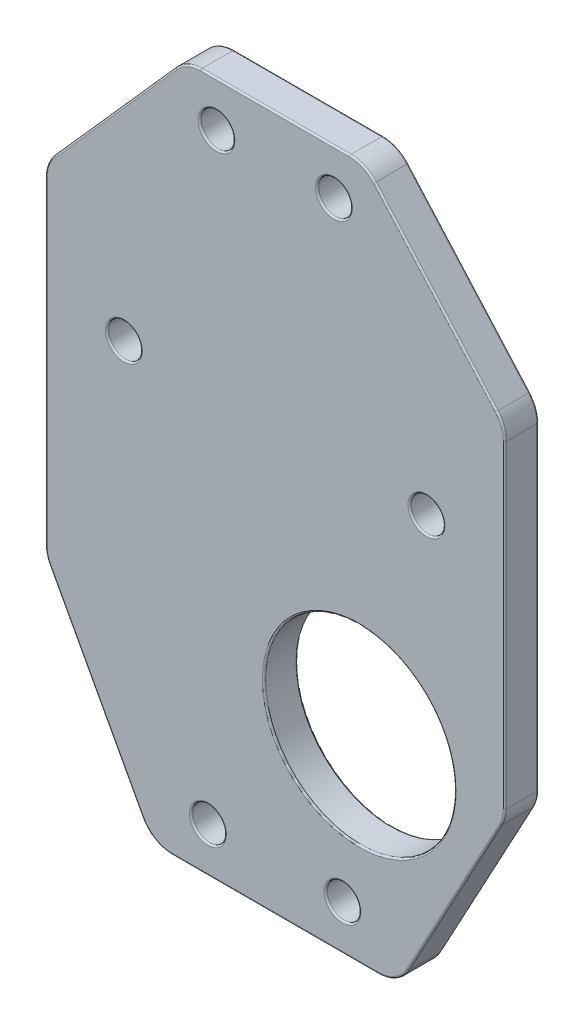
SolidWorks part; units mm, degrees
ref_plane "Front Plane" through (0, 0, 0) normal (0, 0, 1) x (1, 0, 0)
ref_plane "Top Plane" through (0, 0, 0) normal (0, 1, 0) x (1, 0, 0)
ref_plane "Right Plane" through (0, 0, 0) normal (1, 0, 0) x (0, 0, -1)
sketch "Sketch1" plane through (0, 0, 0) normal (0, 0, 1) x (1, 0, 0)
  line L0 (0, 0) -> (0, 62) construction
  line L1 (7.9898, 62) -> (-7.9898, 62)
  line L2 (-7.9898, 62) -> (-20.5, 47.8997)
  line L3 (-20.5, 47.8997) -> (-20.5, 17.5997)
  line L4 (-20.5, 17.5997) -> (-11, 0)
  line L5 (-11, 0) -> (0, 0)
  line L6 (20.5, 17.5997) -> (11, 0)
  line L7 (20.5, 47.8997) -> (20.5, 17.5997)
  line L8 (7.9898, 62) -> (20.5, 47.8997)
  line L9 (7.5, 17.5997) -> (20.5, 17.5997) construction
  line L10 (-13.5, 37.5997) -> (13.5, 37.5997) construction
  line L19 (0, 0) -> (11, 0)
  circle A0 centre (-6, 4) radius 1.5
  circle A1 centre (-13.5, 37.5997) radius 1.5
  circle A2 centre (-5.2398, 58) radius 1.5
  circle A3 centre (5.2398, 58) radius 1.5
  circle A4 centre (13.5, 37.5997) radius 1.5
  circle A5 centre (6, 4) radius 1.5
  circle A6 centre (7.5, 17.5997) radius 8.5
  circle A7 centre (7.5, 17.5997) radius 12 construction
  circle A8 centre (13.5, 37.5997) radius 5 construction
  circle A9 centre (-13.5, 37.5997) radius 5 construction
  dimension "D7" = 3
  dimension "D11" = 4
  dimension "D13" = 10.3
  dimension "D14" = 17
  dimension "D1" = 62
  dimension "D2" = 11
  dimension "D3" = 20
  dimension "D4" = 30.3
  dimension "D5" = 18.85
  dimension "D6" = 20.5
  dimension "D8" = 4
  dimension "D9" = 2.75
  dimension "D10" = 6
  dimension "D12" = 7
  dimension "D15" = 13
  dimension "D16" = 3.5
  dimension "D17" = 3.5
  dimension "D18" = 3.5
extrude "Boss-Extrude1" add sketch "Sketch1" along normal blind 3
fillet "Fillet1" radius 3 8 edges at (-11, 0, 1.5) (-20.5, 17.5997, 1.5) (-20.5, 47.8997, 1.5) (-7.9898, 62, 1.5) (7.9898, 62, 1.5) (20.5, 47.8997, 1.5) (11, 0, 1.5) (20.5, 17.5997, 1.5)
fillet "Fillet2" radius 0.15 46 edges at (16, 17.5997, 0) (12, 37.5997, 0) (-3.7398, 58, 0) (-4.5, 4, 0) (10.7472, 0.4237, 0) (15.9951, 9.2539, 0) (20.4086, 17.6228, 0) (20.5, 32.5592, 0) (20.3047, 47.8256, 0) (14.3146, 54.8714, 0) (7.8712, 61.7361, 0) (0, 62, 0) (-7.8712, 61.7361, 0) (-14.3146, 54.8714, 0) (-20.3047, 47.8256, 0) (-20.5, 32.5592, 0) (-20.4086, 17.6228, 0) (-15.9951, 9.2539, 0) (-10.7472, 0.4237, 0) (0, 0, 0) (-12, 37.5997, 0) (3.7398, 58, 0) (4.5, 4, 0) (16, 17.5997, 3) (12, 37.5997, 3) (-3.7398, 58, 3) (-4.5, 4, 3) (-20.4086, 17.6228, 3) (-20.5, 32.5592, 3) (-20.3047, 47.8256, 3) (-14.3146, 54.8714, 3) (-7.8712, 61.7361, 3) (0, 62, 3) (7.8712, 61.7361, 3) (14.3146, 54.8714, 3) (20.3047, 47.8256, 3) (20.5, 32.5592, 3) (20.4086, 17.6228, 3) (15.9951, 9.2539, 3) (10.7472, 0.4237, 3) (0, 0, 3) (-10.7472, 0.4237, 3) (-15.9951, 9.2539, 3) (-12, 37.5997, 3) (3.7398, 58, 3) (4.5, 4, 3)
